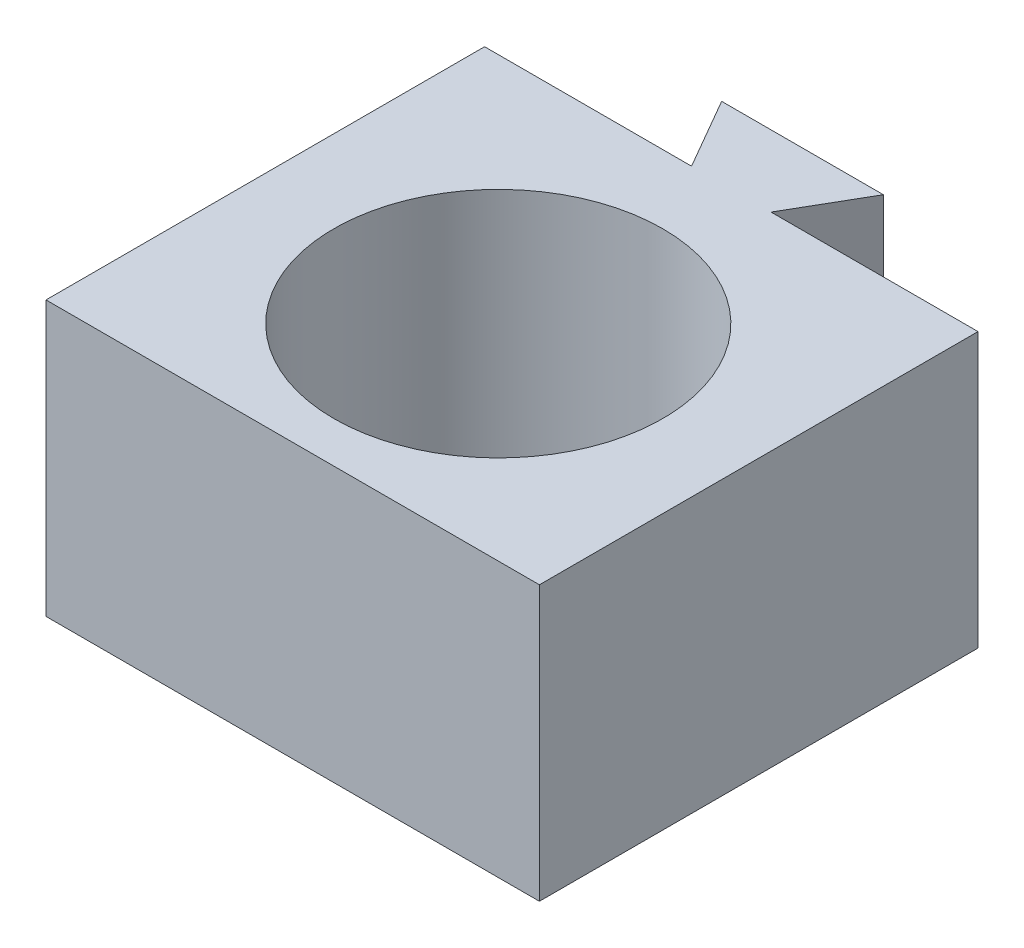
SolidWorks part; units mm, degrees
ref_plane "Front Plane" through (0, 0, 0) normal (0, 0, 1) x (1, 0, 0)
ref_plane "Top Plane" through (0, 0, 0) normal (0, 1, 0) x (1, 0, 0)
ref_plane "Right Plane" through (0, 0, 0) normal (1, 0, 0) x (0, 0, -1)
sketch "Sketch1" plane through (0, 0, 0) normal (0, 0, 1) x (1, 0, 0)
  line L0 (-6, 0) -> (6, 0) construction
  line L1 (-9, -5) -> (9, -5)
  line L2 (-9, -5) -> (-9, 5)
  line L3 (-9, 5) -> (9, 5)
  line L4 (9, -5) -> (9, 5)
  line L5 (-9, -5) -> (9, 5) construction
  line L6 (-9, 5) -> (9, -5) construction
  point P0 (0, 0)
  point P9 (0, 0)
  dimension "D1" = 12
  dimension "D2" = 18
  dimension "D3" = 10
extrude "Boss-Extrude1" add sketch "Sketch1" along normal blind 16
sketch "Sketch6" plane through (0, 5, 0) normal (0, 1, 0) x (1, 0, 0)
  line L0 (9, -16) -> (-9, -16) construction
  line L1 (0, -8.5) -> (0, 0) construction
  line L2 (9, 0) -> (-9, 0) construction
  circle A0 centre (0, -8.5) radius 6
  point P2 (0, -14.5)
  dimension "D1" = 12
  dimension "D2" = 1.5
extrude "Cut-Extrude1" cut sketch "Sketch6" against normal through all
sketch "Sketch8" plane through (0, 5, 0) normal (0, 1, 0) x (1, 0, 0)
  line L0 (-1.45, 0) -> (-2.95, 2.5981)
  line L1 (9, 0) -> (-9, 0) construction
  line L2 (-2.95, 2.5981) -> (2.95, 2.5981)
  line L3 (2.95, 2.5981) -> (1.45, 0)
  line L4 (1.45, 0) -> (-1.45, 0)
  line L5 (0, 0) -> (0, 2.5981) construction
  point P9 (0, 1.8553)
  point P10 (0, 1.8058)
  dimension "D1" = 5.9
  dimension "D2" = 60
  dimension "D3" = 2.9
extrude "Boss-Extrude2" add sketch "Sketch8" against normal offset from surface (8 mm away) 2 up to face at (0, -5, 14.5)
